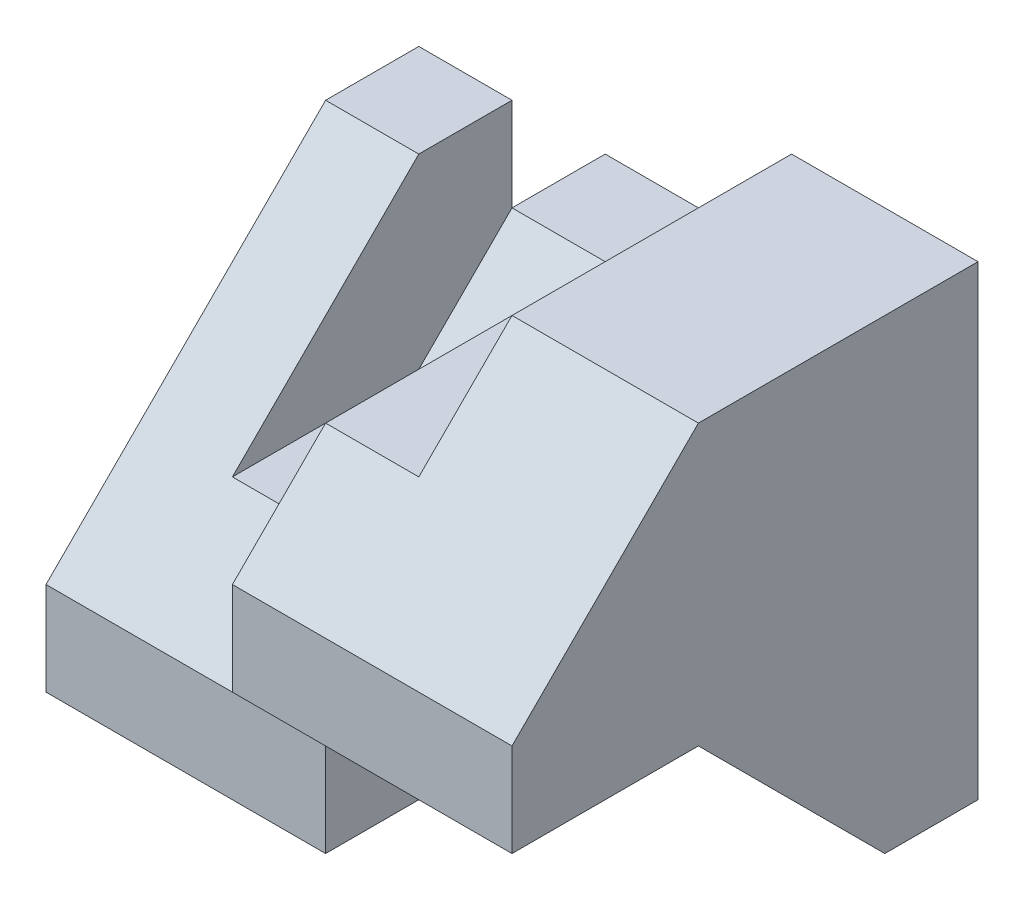
SolidWorks part; units mm, degrees
ref_plane "Front Plane" through (0, 0, 0) normal (0, 0, 1) x (1, 0, 0)
ref_plane "Top Plane" through (0, 0, 0) normal (0, 1, 0) x (1, 0, 0)
ref_plane "Right Plane" through (0, 0, 0) normal (1, 0, 0) x (0, 0, -1)
sketch "Sketch1" plane through (0, 0, 0) normal (0, 0, 1) x (1, 0, 0)
  line L1 (0, 0) -> (60, 0)
  line L2 (0, 0) -> (0, 50)
  line L3 (0, 50) -> (60, 50)
  line L4 (60, 0) -> (60, 50)
  dimension "D1" = 60
  dimension "D2" = 50
extrude "Boss-Extrude1" add sketch "Sketch1" along normal blind 50
sketch "Sketch2" plane through (0, 0, 50) normal (0, 0, 1) x (1, 0, 0)
  line L1 (0, 50) -> (40, 50)
  line L2 (0, 50) -> (0, 40)
  line L3 (0, 40) -> (40, 40)
  line L4 (40, 50) -> (40, 40)
  dimension "D1" = 40
  dimension "D2" = 10
extrude "Cut-Extrude1" cut sketch "Sketch2" against normal blind 50
sketch "Sketch3" plane through (0, 0, 50) normal (0, 0, 1) x (1, 0, 0)
  line L0 (0, 40) -> (40, 40) construction
  line L1 (10, 40) -> (20, 40)
  line L2 (10, 40) -> (10, 20)
  line L3 (10, 20) -> (20, 20)
  line L4 (20, 40) -> (20, 20)
  dimension "D1" = 10
  dimension "D2" = 20
  dimension "D3" = 10
extrude "Cut-Extrude2" cut sketch "Sketch3" against normal blind 50
sketch "Sketch4" plane through (0, 0, 50) normal (0, 0, 1) x (1, 0, 0)
  line L0 (0, 40) -> (10, 40)
  line L1 (10, 40) -> (10, 20)
  line L2 (10, 20) -> (20, 20)
  line L3 (20, 20) -> (20, 40)
  line L4 (20, 40) -> (30, 40)
  line L5 (20, 40) -> (40, 40) construction
  line L6 (30, 40) -> (30, 10)
  line L7 (30, 10) -> (0, 10)
  line L8 (0, 40) -> (0, 0) construction
  line L9 (0, 10) -> (0, 40)
  dimension "D1" = 30
  dimension "D2" = 10
extrude "Cut-Extrude3" cut sketch "Sketch4" against normal blind 40
sketch "Sketch5" plane through (0, 0, 10) normal (0, 0, 1) x (1, 0, 0)
  line L0 (0, 10) -> (30, 10) construction
  line L1 (20, 20) -> (10, 20)
  line L2 (20, 20) -> (20, 10)
  line L3 (20, 10) -> (10, 10)
  line L4 (10, 20) -> (10, 10)
  dimension "D1" = 10
extrude "Boss-Extrude2" add sketch "Sketch5" along normal blind 20
sketch "Sketch6" plane through (0, 10, 0) normal (0, 1, 0) x (1, 0, 0)
  line L1 (0, -50) -> (30, -50)
  line L2 (0, -50) -> (0, -40)
  line L3 (0, -40) -> (30, -40)
  line L4 (30, -50) -> (30, -40)
  dimension "D1" = 10
  dimension "D2" = 30
extrude "Cut-Extrude4" cut sketch "Sketch6" against normal blind 20
sketch "Sketch7" plane through (0, 0, 50) normal (0, 0, 1) x (1, 0, 0)
  line L0 (60, 0) -> (60, 50) construction
  line L1 (60, 30) -> (30, 30)
  line L2 (60, 30) -> (60, 20)
  line L3 (60, 20) -> (30, 20)
  line L4 (30, 30) -> (30, 20)
  line L5 (30, 0) -> (30, 40) construction
  dimension "D1" = 10
  dimension "D2" = 20
extrude "Cut-Extrude7" cut sketch "Sketch7" against normal blind 10
sketch "Sketch15" plane through (0, 0, 0) normal (0, 0, -1) x (-1, 0, 0)
  line L1 (-40, 40) -> (-30, 40)
  line L2 (-40, 40) -> (-40, 30)
  line L3 (-40, 30) -> (-30, 30)
  line L4 (-30, 40) -> (-30, 30)
  dimension "D1" = 10
  dimension "D2" = 10
extrude "Cut-Extrude25" cut sketch "Sketch15" against normal blind 39
sketch "Sketch16" plane through (0, 0, 39) normal (0, 0, -1) x (-1, 0, 0)
  line L1 (-30, 30) -> (-40, 30)
  line L2 (-30, 30) -> (-30, 40)
  line L3 (-30, 40) -> (-40, 40)
  line L4 (-40, 30) -> (-40, 40)
extrude "Cut-Extrude30" cut sketch "Sketch16" against normal blind 0.9999
sketch "Sketch19" plane through (60, 0, 0) normal (1, 0, 0) x (0, 0, -1)
  line L0 (-30, 50) -> (-50, 30)
  line L1 (-50, 50) -> (0, 50) construction
  line L2 (-50, 30) -> (-50, 50) construction
  line L3 (-50, 30) -> (-50, 50)
  line L4 (-30, 50) -> (-50, 50)
  dimension "D1" = 30
  dimension "D2" = 20
extrude "Cut-Extrude36" cut sketch "Sketch19" against normal blind 30
sketch "Sketch26" plane through (0, 0, 30) normal (0, 0, 1) x (1, 0, 0)
  line L1 (10, 20) -> (20, 20)
  line L2 (10, 20) -> (10, 10)
  line L3 (10, 10) -> (20, 10)
  line L4 (20, 20) -> (20, 10)
extrude "Cut-Extrude37" cut sketch "Sketch26" against normal blind 20
sketch "Sketch27" plane through (40, 0, 0) normal (-1, 0, 0) x (0, 0, 1)
  line L0 (0, 30) -> (0, 50) construction
  line L1 (39.9999, 30) -> (0, 30)
  line L2 (39.9999, 30) -> (39.9999, 40)
  line L3 (39.9999, 40) -> (0, 40)
  line L4 (0, 30) -> (0, 40)
  dimension "D1" = 10
extrude "Boss-Extrude22" add sketch "Sketch27" along normal blind 10
sketch "Sketch28" plane through (30, 0, 0) normal (-1, 0, 0) x (0, 0, 1)
  line L0 (40, 10) -> (10, 40)
  line L1 (10, 40) -> (10, 10)
  line L2 (10, 10) -> (40, 10)
extrude "Boss-Extrude24" add sketch "Sketch28" along normal blind 30
sketch "Sketch29" plane through (0, 0, 10) normal (0, 0, -1) x (-1, 0, 0)
  line L1 (-20, 40) -> (-10, 40)
  line L2 (-20, 40) -> (-20, 20)
  line L3 (-20, 20) -> (-10, 20)
  line L4 (-10, 40) -> (-10, 20)
extrude "Cut-Extrude38" cut sketch "Sketch29" against normal blind 30
sketch "Sketch30" plane through (30, 0, 0) normal (-1, 0, 0) x (0, 0, 1)
  line L1 (40, 30) -> (50, 30)
  line L2 (40, 30) -> (40, 20)
  line L3 (40, 20) -> (50, 20)
  line L4 (50, 30) -> (50, 20)
extrude "Boss-Extrude25" add sketch "Sketch30" against normal blind 30
sketch "Sketch31" plane through (30, 0, 0) normal (-1, 0, 0) x (0, 0, 1)
  line L0 (40, 0) -> (40, 10)
  line L1 (40, 10) -> (30, 20)
  line L2 (40, 10) -> (10, 40) construction
  line L3 (30, 20) -> (50, 20)
  line L4 (50, 0) -> (50, 30) construction
  line L5 (50, 20) -> (50, 0)
  line L6 (50, 0) -> (40, 0)
  dimension "D1" = 20
extrude "Cut-Extrude39" cut sketch "Sketch31" against normal blind 30
sketch "Sketch33" plane through (60, 0, 0) normal (1, 0, 0) x (0, 0, -1)
  line L0 (-30, 20) -> (-10, 0)
  line L1 (-40, 0) -> (0, 0) construction
  line L2 (-10, 0) -> (-10, 20)
  line L3 (-10, 20) -> (-30, 20)
  line L4 (-30, 20) -> (-40, 10)
  line L5 (-40, 10) -> (-40, 0)
  line L6 (-40, 0) -> (-10, 0)
  line M4 (-30, 20) -> (-40, 10)
  line M5 (-40, 10) -> (-40, 0)
  line M6 (-40, 0) -> (0, 0)
  dimension "D1" = 10
extrude "Cut-Extrude42" cut sketch "Sketch33" against normal blind 30 contours L0 M4 M5 M6
sketch "Sketch34" plane through (0, 40, 0) normal (0, 1, 0) x (1, 0, 0)
  line L0 (20, 0) -> (40, 0) construction
  line L1 (20, -10) -> (30, -10)
  line L2 (20, -10) -> (20, 0)
  line L3 (20, 0) -> (30, 0)
  line L4 (30, -10) -> (30, 0)
extrude "Cut-Extrude43" cut sketch "Sketch34" against normal blind 0.0001
